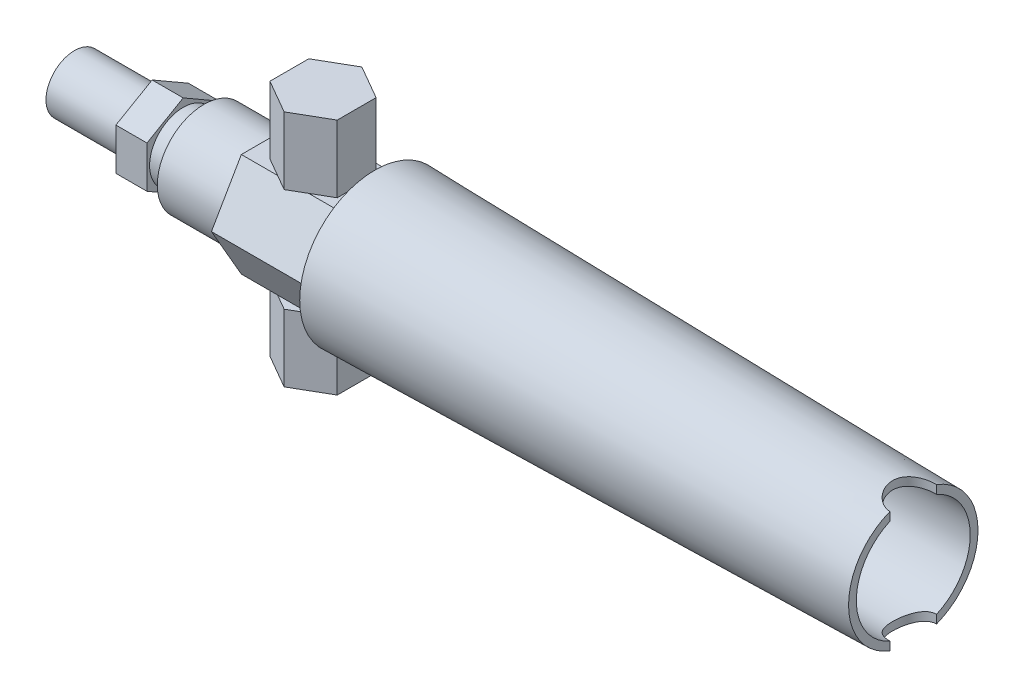
SolidWorks part; units mm, degrees
ref_plane "Front Plane" through (0, 0, 0) normal (0, 0, 1) x (1, 0, 0)
ref_plane "Top Plane" through (0, 0, 0) normal (0, 1, 0) x (1, 0, 0)
ref_plane "Right Plane" through (0, 0, 0) normal (1, 0, 0) x (0, 0, -1)
sketch "Sketch1" plane through (0, 0, 0) normal (0, 0, 1) x (1, 0, 0)
  line L0 (0, 0) -> (162, 0)
  line L1 (0, 0) -> (0, 5.5)
  line L2 (0, 5.5) -> (15, 5.5)
  line L3 (15, 5.5) -> (15, 6.5)
  line L4 (15, 6.5) -> (25, 6.5)
  line L5 (25, 6.5) -> (25, 9)
  line L6 (25, 9) -> (58, 9)
  line L7 (58, 9) -> (58, 14.5)
  line L8 (58, 14.5) -> (162, 12.5)
  line L9 (162, 12.5) -> (162, 0)
  dimension "D1" = 5.5
  dimension "D2" = 15
  dimension "D3" = 6.5
  dimension "D4" = 10
  dimension "D5" = 9
  dimension "D6" = 33
  dimension "D7" = 104
  dimension "D8" = 14.5
  dimension "D9" = 12.5
  dimension "D10" = 162
revolve "Revolve1" add sketch "Sketch1" angle 360 about L0
sketch "Sketch2" plane through (15, 0, 0) normal (-1, 0, 0) x (0, 0, 1)
  line L1 (0, 8.0829) -> (-7, 4.0415)
  line L2 (-7, 4.0415) -> (-7, -4.0415)
  line L3 (-7, -4.0415) -> (0, -8.0829)
  line L4 (0, -8.0829) -> (7, -4.0415)
  line L5 (7, -4.0415) -> (7, 4.0415)
  line L6 (7, 4.0415) -> (0, 8.0829)
  circle A0 centre (0, 0) radius 7 construction
  dimension "D1" = 14
extrude "Boss-Extrude1" add sketch "Sketch2" against normal blind 6
sketch "Sketch3" plane through (58, 0, 0) normal (-1, 0, 0) x (0, 0, 1)
  line L7 (5.7735, 10) -> (-5.7735, 10)
  line L8 (-5.7735, 10) -> (-11.547, 0)
  line L9 (-11.547, 0) -> (-5.7735, -10)
  line L10 (-5.7735, -10) -> (5.7735, -10)
  line L11 (5.7735, -10) -> (11.547, 0)
  line L12 (11.547, 0) -> (5.7735, 10)
  circle A0 centre (0, 0) radius 10 construction
  dimension "D1" = 20
extrude "Boss-Extrude2" add sketch "Sketch3" along normal blind 20
sketch "Sketch4" plane through (0, 0, 0) normal (0, 1, 0) x (1, 0, 0)
  line L0 (162, -12.5) -> (162, 12.5) construction
  ellipse E0 centre (162, 0) end of major axis (162, 4.5) minor radius 4
  dimension "D1" = 9
  dimension "D2" = 8
extrude "Cut-Extrude1" cut sketch "Sketch4" along normal mid plane 30
sketch "Sketch5" plane through (162, 0, 0) normal (1, 0, 0) x (0, 0, -1)
  circle A0 centre (0, 0) radius 11
  dimension "D1" = 22
extrude "Cut-Extrude2" cut sketch "Sketch5" against normal blind 30
sketch "Sketch6" plane through (0, 10, 0) normal (0, -1, 0) x (1, 0, 0)
  line L0 (38, 0) -> (58, 0) construction
  line L2 (58, 14.5) -> (58, -14.5) construction
  line L4 (48, 7.5056) -> (41.5, 3.7528)
  line L5 (41.5, 3.7528) -> (41.5, -3.7528)
  line L6 (41.5, -3.7528) -> (48, -7.5056)
  line L7 (48, -7.5056) -> (54.5, -3.7528)
  line L8 (54.5, -3.7528) -> (54.5, 3.7528)
  line L9 (54.5, 3.7528) -> (48, 7.5056)
  circle A0 centre (48, 0) radius 6.5 construction
  dimension "D1" = 13
extrude "Boss-Extrude3" add sketch "Sketch6" against normal blind 13
mirror "Mirror1" about plane through (0, 0, 0) normal (0, 1, 0) of "Boss-Extrude3"
